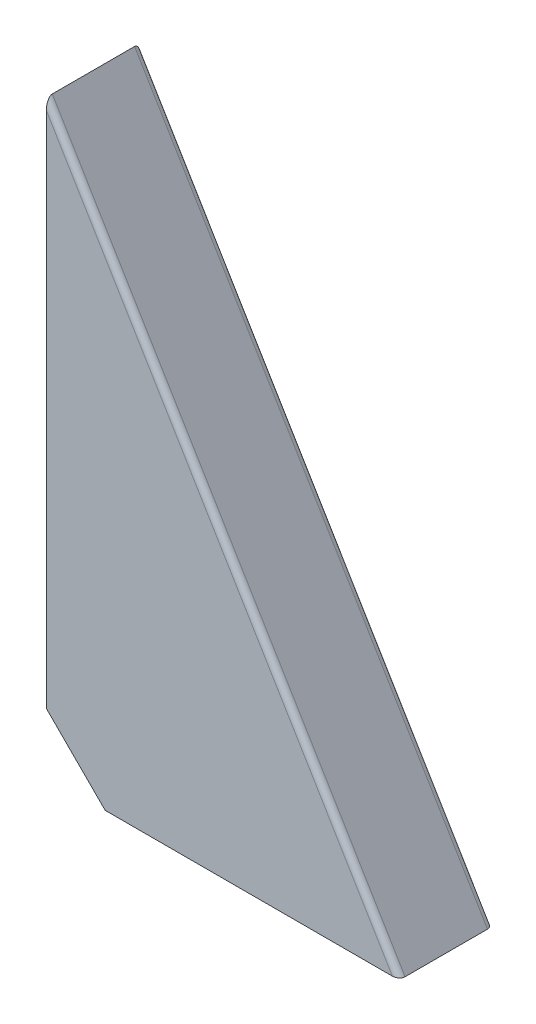
SolidWorks part; units mm, degrees
ref_plane "Front Plane" through (0, 0, 0) normal (0, 0, 1) x (1, 0, 0)
ref_plane "Top Plane" through (0, 0, 0) normal (0, 1, 0) x (1, 0, 0)
ref_plane "Right Plane" through (0, 0, 0) normal (1, 0, 0) x (0, 0, -1)
sketch "Sketch1" plane through (0, 0, 0) normal (0, 0, 1) x (1, 0, 0)
  line L0 (0, 0) -> (60, 0)
  line L1 (60, 0) -> (0, 100)
  line L2 (0, 100) -> (0, 0)
  dimension "D1" = 100
  dimension "D2" = 60
extrude "Boss-Extrude1" add sketch "Sketch1" along normal mid plane 16
sketch "Sketch2" plane through (0, 0, 8) normal (0, 0, 1) x (1, 0, 0)
  line L0 (0, 0) -> (0, 10)
  line L1 (0, 100) -> (0, 0) construction
  line L2 (0, 10) -> (10, 0)
  line L3 (0, 0) -> (60, 0) construction
  line L4 (10, 0) -> (0, 0)
  dimension "D1" = 10
  dimension "D2" = 10
extrude "Cut-Extrude1" cut sketch "Sketch2" against normal through all
fillet "Fillet1" radius 1 2 edges at (30, 50, 8) (30, 50, -8)
